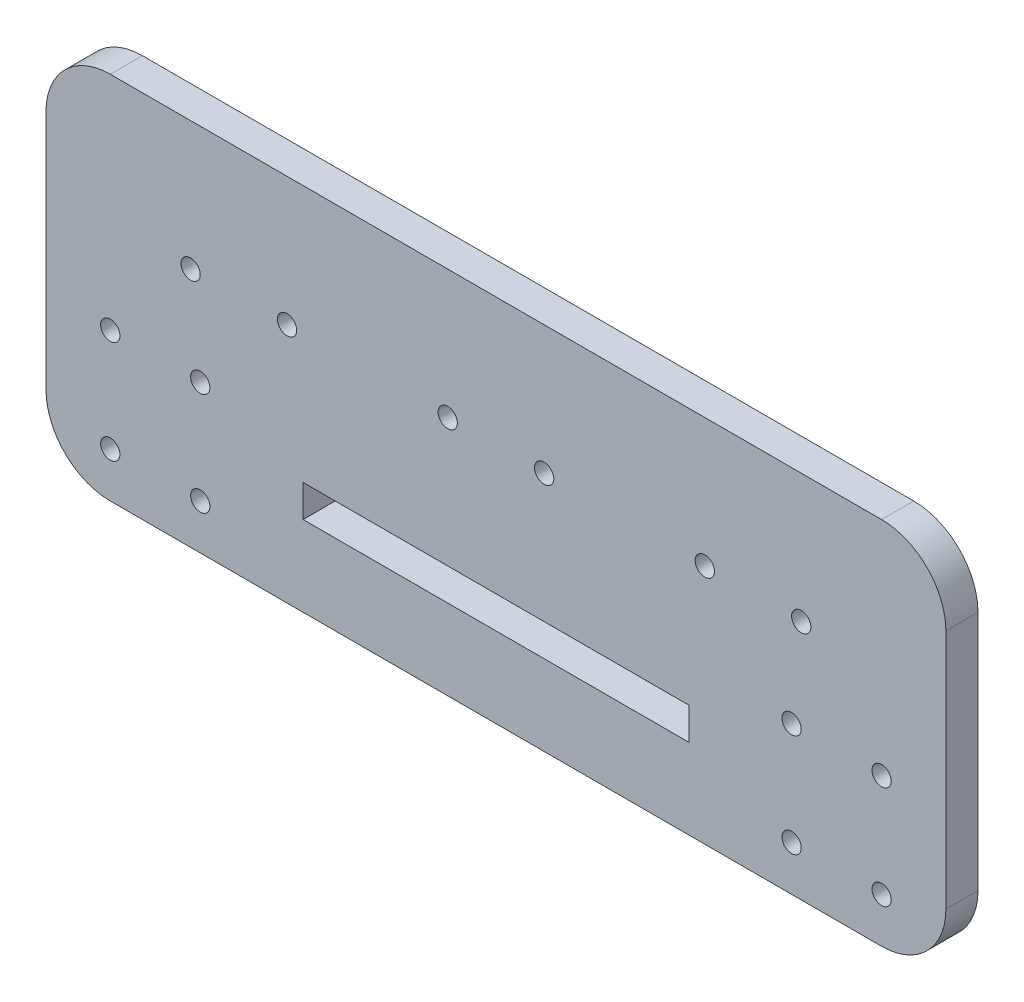
SolidWorks part; units mm, degrees
ref_plane "Front Plane" through (0, 0, 0) normal (0, 0, 1) x (1, 0, 0)
ref_plane "Top Plane" through (0, 0, 0) normal (0, 1, 0) x (1, 0, 0)
ref_plane "Right Plane" through (0, 0, 0) normal (1, 0, 0) x (0, 0, -1)
sketch "Sketch1" plane through (0, 0, 0) normal (0, 0, 1) x (1, 0, 0)
  line L1 (-60, 28.75) -> (60, 28.75)
  line L2 (-70, 18.75) -> (-70, -18.75)
  line L3 (-60, -28.75) -> (60, -28.75)
  line L4 (70, 18.75) -> (70, -18.75)
  line L5 (-70, 28.75) -> (70, -28.75) construction
  line L6 (-70, -28.75) -> (70, 28.75) construction
  arc A0 (-70, -18.75) -> (-60, -28.75) centre (-60, -18.75) ccw
  arc A1 (60, -28.75) -> (70, -18.75) centre (60, -18.75) ccw
  arc A2 (60, 28.75) -> (70, 18.75) centre (60, 18.75) cw
  arc A3 (-60, 28.75) -> (-70, 18.75) centre (-60, 18.75) ccw
  point P0 (0, 0)
  dimension "D3" = 10
  dimension "D1" = 57.5
  dimension "D2" = 140
extrude "Boss-Extrude1" add sketch "Sketch1" along normal blind 5
sketch "Sketch2" plane through (0, 0, 5) normal (0, 0, 1) x (1, 0, 0)
  line L0 (0, 28.75) -> (0, -28.75) construction
  line L1 (60, 28.75) -> (-60, 28.75) construction
  line L2 (-60, -28.75) -> (60, -28.75) construction
  line L3 (70, -18.75) -> (70, -13.75) construction
  line L4 (70, -18.75) -> (70, 18.75) construction
  line L5 (70, -13.75) -> (53, -13.75) construction
  line L6 (53, -13.75) -> (0, -13.75) construction
  line L7 (46, -5.75) -> (60, -5.75) construction
  line L8 (46, -5.75) -> (46, -21.75) construction
  line L9 (46, -21.75) -> (60, -21.75) construction
  line L10 (60, -5.75) -> (60, -21.75) construction
  line L11 (46, -5.75) -> (60, -21.75) construction
  line L12 (46, -21.75) -> (60, -5.75) construction
  line L14 (-30, -11.25) -> (30, -11.25)
  line L15 (-30, -11.25) -> (-30, -16.25)
  line L16 (-30, -16.25) -> (30, -16.25)
  line L17 (30, -11.25) -> (30, -16.25)
  line L18 (-30, -11.25) -> (30, -16.25) construction
  line L19 (-30, -16.25) -> (30, -11.25) construction
  circle A0 centre (60, -5.75) radius 1.5
  circle A1 centre (46, -5.75) radius 1.5
  circle A2 centre (46, -21.75) radius 1.5
  circle A3 centre (60, -21.75) radius 1.5
  circle A4 centre (-46, -5.75) radius 1.5
  circle A5 centre (-46, -21.75) radius 1.5
  circle A6 centre (-60, -21.75) radius 1.5
  circle A7 centre (-60, -5.75) radius 1.5
  dimension "D5" = 3
  dimension "D6" = 3
  dimension "D7" = 3
  dimension "D8" = 3
  dimension "D1" = 5
  dimension "D2" = 17
  dimension "D3" = 16
  dimension "D4" = 14
  dimension "D9" = 5
  dimension "D10" = 60
extrude "Cut-Extrude1" cut sketch "Sketch2" against normal blind 5
sketch "Sketch4" plane through (0, 0, 5) normal (0, 0, 1) x (1, 0, 0)
  line L0 (0, -11.25) -> (0, 8.75) construction
  line L1 (30, -11.25) -> (-30, -11.25) construction
  line L2 (0, 8.75) -> (7.5, 8.75) construction
  line L3 (0, 28.75) -> (40, 28.75) construction
  line L4 (60, 28.75) -> (-60, 28.75) construction
  line L5 (40, 28.75) -> (40, 8.75) construction
  line L6 (40, 8.75) -> (47.5, 8.75) construction
  circle A0 centre (7.5, 8.75) radius 1.5
  circle A1 centre (-7.5, 8.75) radius 1.5
  circle A2 centre (47.5, 8.75) radius 1.5
  circle A3 centre (32.5, 8.75) radius 1.5
  circle A4 centre (-32.5, 8.75) radius 1.5
  circle A5 centre (-47.5, 8.75) radius 1.5
  dimension "D3" = 3
  dimension "D7" = 3
  dimension "D1" = 20
  dimension "D2" = 7.5
  dimension "D4" = 40
  dimension "D5" = 20
  dimension "D6" = 7.5
extrude "Cut-Extrude2" cut sketch "Sketch4" against normal blind 5
